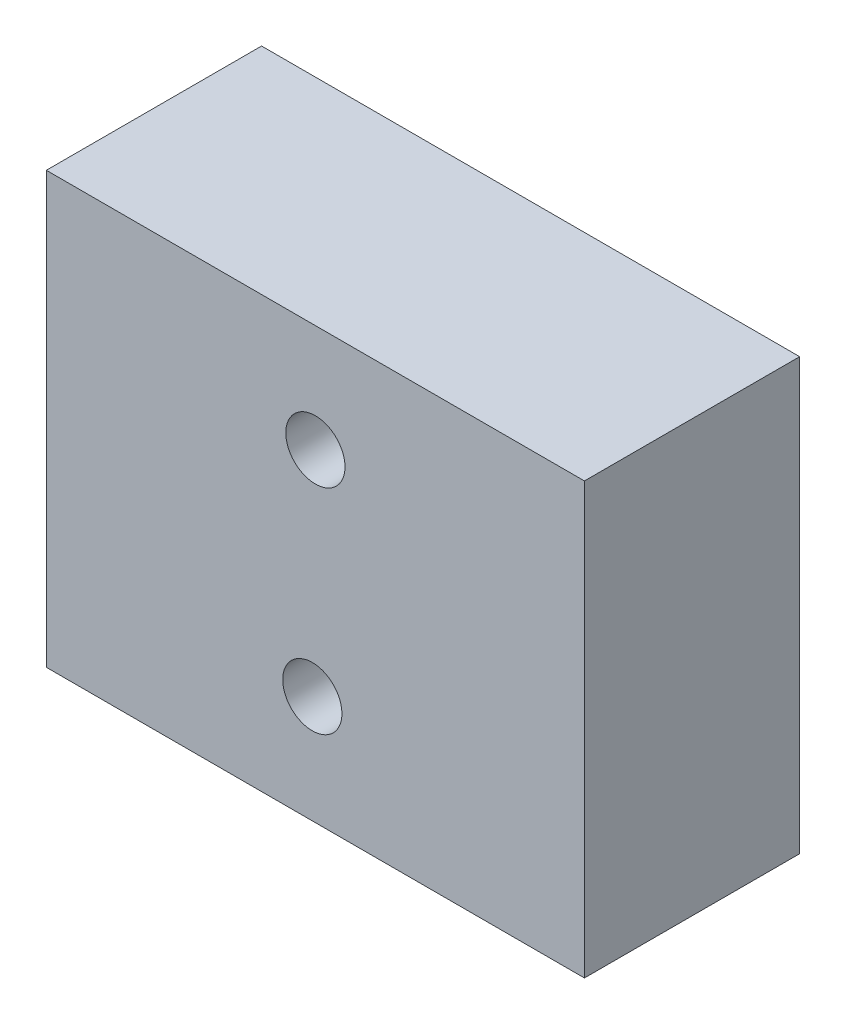
SolidWorks part; units mm, degrees
ref_plane "Front Plane" through (0, 0, 0) normal (0, 0, 1) x (1, 0, 0)
ref_plane "Top Plane" through (0, 0, 0) normal (0, 1, 0) x (1, 0, 0)
ref_plane "Right Plane" through (0, 0, 0) normal (1, 0, 0) x (0, 0, -1)
sketch "Sketch1" plane through (0, 0, 0) normal (0, 1, 0) x (1, 0, 0)
  line L1 (0, 0) -> (50, 0)
  line L2 (0, 0) -> (0, 20)
  line L3 (0, 20) -> (50, 20)
  line L4 (50, 0) -> (50, 20)
  dimension "D1" = 50
  dimension "D2" = 20
extrude "Boss-Extrude1" add sketch "Sketch1" along normal blind 40
hole_wizard "M5 Clearance Hole1" positions "Sketch2" profile "Sketch3" hole size "M5" standard "ANSI Metric" end condition through all
sketch "Sketch2" plane through (0, 0, 0) normal (0, 0, 1) x (1, 0, 0)
  line L0 (0, 40) -> (50, 40) construction
  line L1 (0, 40) -> (0, 0) construction
  point P0 (25, 30)
  point P2 (24.7158, 10)
  dimension "D1" = 10
  dimension "D2" = 20
  dimension "D3" = 25
sketch "Sketch3" plane through (25, 30, 0) normal (1, 0, 0) x (0, -1, 0)
  line L0 (0, 0) -> (0, 20)
  line L1 (0, 20) -> (2.75, 20)
  line L2 (2.75, 20) -> (2.75, 0)
  line L5 (2.75, 0) -> (0, 0)
  line L11 (0, -6.35) -> (0, 107.95) construction
  dimension "Thru Hole Dia." = 5.5
  dimension "Thru Hole Depth" = 20
hole_wizard "#97 (0.0059) Diameter Hole1" positions "Sketch4" profile "Sketch6" hole size "#97" standard "ANSI Inch"
sketch "Sketch4" plane through (0, 0, 0) normal (0, -1, 0) x (-1, 0, 0)
  line L0 (-50, 0) -> (-50, 20) construction
  line L1 (-50, 20) -> (0, 20) construction
  point P0 (-40, 10)
  point P2 (-9, 10)
  point P7 (0, 0)
  dimension "D1" = 10
  dimension "D2" = 31
  dimension "D3" = 10
sketch "Sketch6" plane through (40, 0, -10) normal (1, 0, 0) x (0, 0, -1)
  line L0 (0, 0) -> (0, 14.3045)
  line L1 (0, 14.3045) -> (3.8354, 12)
  line L2 (3.8354, 12) -> (3.8354, 0.7157)
  line L3 (3.8354, 0.7157) -> (3.8604, 0)
  line L5 (3.8604, 0) -> (0, 0)
  line L6 (-3.8354, 0.7157) -> (-3.8604, 0) construction
  line L10 (0, 14.3045) -> (-3.8354, 12) construction
  line L11 (0, -6.35) -> (0, 107.95) construction
  dimension "Hole Dia." = 7.6708
  dimension "Hole Depth" = 12
  dimension "Near C'Sink Dia." = 7.7208
  dimension "Near C'Sink Angle" = 4
  dimension "Drill Angle" = 118
